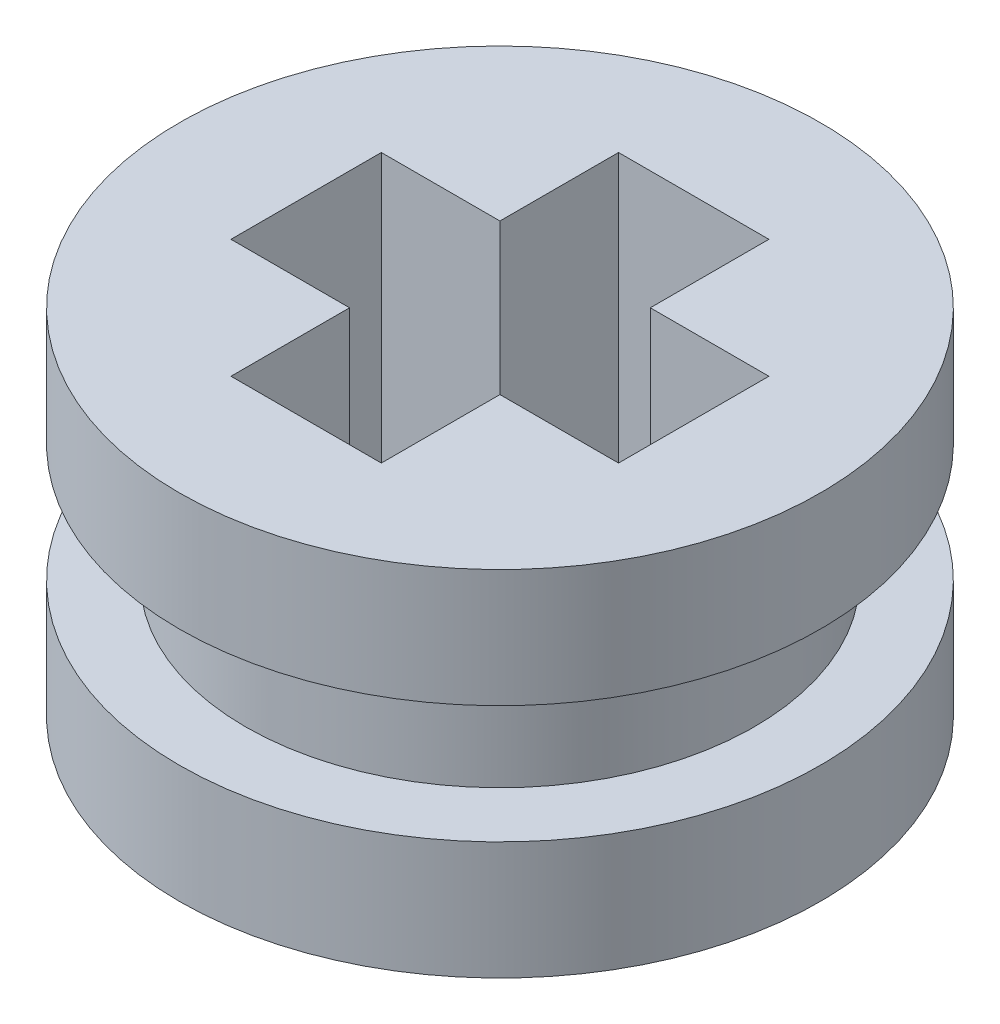
SolidWorks part; units mm, degrees
ref_plane "Front Plane" through (0, 0, 0) normal (0, 0, 1) x (1, 0, 0)
ref_plane "Top Plane" through (0, 0, 0) normal (0, 1, 0) x (1, 0, 0)
ref_plane "Right Plane" through (0, 0, 0) normal (1, 0, 0) x (0, 0, -1)
sketch "Sketch2" plane through (0, 0, 0) normal (0, 1, 0) x (1, 0, 0)
  circle A0 centre (0, 0) radius 3.625
  dimension "D1" = 7.25
extrude "Boss-Extrude1" add sketch "Sketch2" along normal blind 1.3333
sketch "Sketch6" plane through (0, 1.3333, 0) normal (0, 1, 0) x (1, 0, 0)
  circle A0 centre (0, 0) radius 2.875
  dimension "D1" = 5.75
extrude "Boss-Extrude2" add sketch "Sketch6" along normal blind 1.3333
sketch "Sketch7" plane through (0, 2.6667, 0) normal (0, 1, 0) x (1, 0, 0)
  circle A0 centre (0, 0) radius 3.625
  dimension "D1" = 7.25
extrude "Boss-Extrude3" add sketch "Sketch7" along normal blind 1.3333
sketch "Sketch8" plane through (0, 4, 0) normal (0, 1, 0) x (1, 0, 0)
  line L0 (-0.85, 0.85) -> (-2.1909, 0.85)
  line L1 (-0.85, -2.1909) -> (0.85, -2.1909)
  line L2 (-0.85, -2.1909) -> (-0.85, -0.85)
  line L3 (-0.85, 2.1909) -> (0.85, 2.1909)
  line L4 (0.85, -2.1909) -> (0.85, -0.85)
  line L5 (-0.85, -0.85) -> (-2.1909, -0.85)
  line L6 (0.85, 0.85) -> (0.85, 2.1909)
  line L7 (2.1909, -0.85) -> (0.85, -0.85)
  line L8 (2.1909, -0.85) -> (2.1909, 0.85)
  line L9 (2.1909, 0.85) -> (0.85, 0.85)
  line L10 (-2.1909, -0.85) -> (-2.1909, 0.85)
  line L11 (-0.85, 0.85) -> (-0.85, 2.1909)
  circle A0 centre (0, 0) radius 2.35
  dimension "D1" = 4.7
  dimension "D2" = 1.7
  dimension "D3" = 1.7
extrude "Cut-Extrude1" cut sketch "Sketch8" against normal through all contours L11 L0 L10 L5 L2 L1 L4 L7 L8 L9 L6 L3
